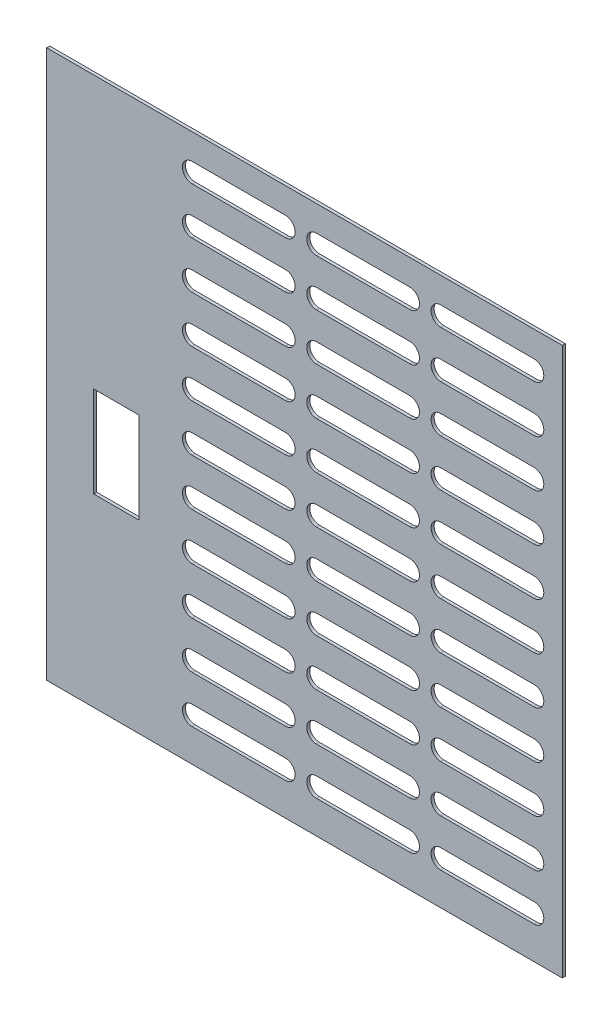
SolidWorks part; units mm, degrees
ref_plane "Plano frontal" through (0, 0, 0) normal (0, 0, 1) x (1, 0, 0)
ref_plane "Plano superior" through (0, 0, 0) normal (0, 1, 0) x (1, 0, 0)
ref_plane "Plano direito" through (0, 0, 0) normal (1, 0, 0) x (0, 0, -1)
sketch "Esboço1" plane through (0, 0, 0) normal (0, 0, 1) x (1, 0, 0)
  line L0 (-116.056, 178.9748) -> (-85.2858, 178.9748) construction
  line L1 (-205, 190.6547) -> (-35, 190.6547)
  line L2 (-205, 190.6547) -> (-205, 10)
  line L3 (-205, 10) -> (-35, 10)
  line L4 (-35, 190.6547) -> (-35, 10)
  line L5 (-116.056, 182.1711) -> (-85.2858, 182.1711)
  line L6 (-116.056, 175.7786) -> (-85.2858, 175.7786)
  line L7 (-75.056, 178.9748) -> (-44.2858, 178.9748) construction
  line L8 (-75.056, 182.1711) -> (-44.2858, 182.1711)
  line L9 (-157.056, 178.9748) -> (-126.2858, 178.9748) construction
  line L10 (-157.056, 182.1711) -> (-126.2858, 182.1711)
  line L11 (-157.056, 175.7786) -> (-126.2858, 175.7786)
  line L12 (-75.056, 175.7786) -> (-44.2858, 175.7786)
  line L13 (-116.056, 163.4748) -> (-85.2858, 163.4748) construction
  line L14 (-116.056, 166.6711) -> (-85.2858, 166.6711)
  line L15 (-116.056, 160.2786) -> (-85.2858, 160.2786)
  line L16 (-75.056, 163.4748) -> (-44.2858, 163.4748) construction
  line L17 (-75.056, 166.6711) -> (-44.2858, 166.6711)
  line L18 (-75.056, 160.2786) -> (-44.2858, 160.2786)
  line L19 (-116.056, 147.9748) -> (-85.2858, 147.9748) construction
  line L20 (-116.056, 151.1711) -> (-85.2858, 151.1711)
  line L21 (-116.056, 144.7786) -> (-85.2858, 144.7786)
  line L22 (-75.056, 147.9748) -> (-44.2858, 147.9748) construction
  line L23 (-75.056, 151.1711) -> (-44.2858, 151.1711)
  line L24 (-75.056, 144.7786) -> (-44.2858, 144.7786)
  line L25 (-116.056, 132.4748) -> (-85.2858, 132.4748) construction
  line L26 (-116.056, 135.6711) -> (-85.2858, 135.6711)
  line L27 (-116.056, 129.2786) -> (-85.2858, 129.2786)
  line L28 (-75.056, 132.4748) -> (-44.2858, 132.4748) construction
  line L29 (-75.056, 135.6711) -> (-44.2858, 135.6711)
  line L30 (-75.056, 129.2786) -> (-44.2858, 129.2786)
  line L31 (-116.056, 116.9748) -> (-85.2858, 116.9748) construction
  line L32 (-116.056, 120.1711) -> (-85.2858, 120.1711)
  line L33 (-116.056, 113.7786) -> (-85.2858, 113.7786)
  line L34 (-75.056, 116.9748) -> (-44.2858, 116.9748) construction
  line L35 (-75.056, 120.1711) -> (-44.2858, 120.1711)
  line L36 (-75.056, 113.7786) -> (-44.2858, 113.7786)
  line L37 (-116.056, 101.4748) -> (-85.2858, 101.4748) construction
  line L38 (-116.056, 104.6711) -> (-85.2858, 104.6711)
  line L39 (-116.056, 98.2786) -> (-85.2858, 98.2786)
  line L40 (-75.056, 101.4748) -> (-44.2858, 101.4748) construction
  line L41 (-75.056, 104.6711) -> (-44.2858, 104.6711)
  line L42 (-75.056, 98.2786) -> (-44.2858, 98.2786)
  line L43 (-116.056, 85.9748) -> (-85.2858, 85.9748) construction
  line L44 (-116.056, 89.1711) -> (-85.2858, 89.1711)
  line L45 (-116.056, 82.7786) -> (-85.2858, 82.7786)
  line L46 (-75.056, 85.9748) -> (-44.2858, 85.9748) construction
  line L47 (-75.056, 89.1711) -> (-44.2858, 89.1711)
  line L48 (-75.056, 82.7786) -> (-44.2858, 82.7786)
  line L49 (-116.056, 70.4748) -> (-85.2858, 70.4748) construction
  line L50 (-116.056, 73.6711) -> (-85.2858, 73.6711)
  line L51 (-116.056, 67.2786) -> (-85.2858, 67.2786)
  line L52 (-75.056, 70.4748) -> (-44.2858, 70.4748) construction
  line L53 (-75.056, 73.6711) -> (-44.2858, 73.6711)
  line L54 (-75.056, 67.2786) -> (-44.2858, 67.2786)
  line L55 (-116.056, 54.9748) -> (-85.2858, 54.9748) construction
  line L56 (-116.056, 58.1711) -> (-85.2858, 58.1711)
  line L57 (-116.056, 51.7786) -> (-85.2858, 51.7786)
  line L58 (-75.056, 54.9748) -> (-44.2858, 54.9748) construction
  line L59 (-75.056, 58.1711) -> (-44.2858, 58.1711)
  line L60 (-75.056, 51.7786) -> (-44.2858, 51.7786)
  line L61 (-116.056, 39.4748) -> (-85.2858, 39.4748) construction
  line L62 (-116.056, 42.6711) -> (-85.2858, 42.6711)
  line L63 (-116.056, 36.2786) -> (-85.2858, 36.2786)
  line L64 (-75.056, 39.4748) -> (-44.2858, 39.4748) construction
  line L65 (-75.056, 42.6711) -> (-44.2858, 42.6711)
  line L66 (-75.056, 36.2786) -> (-44.2858, 36.2786)
  line L67 (-116.056, 23.9748) -> (-85.2858, 23.9748) construction
  line L68 (-116.056, 27.1711) -> (-85.2858, 27.1711)
  line L69 (-116.056, 20.7786) -> (-85.2858, 20.7786)
  line L70 (-75.056, 23.9748) -> (-44.2858, 23.9748) construction
  line L71 (-75.056, 27.1711) -> (-44.2858, 27.1711)
  line L72 (-75.056, 20.7786) -> (-44.2858, 20.7786)
  line L73 (-157.056, 163.4748) -> (-126.2858, 163.4748) construction
  line L74 (-157.056, 166.6711) -> (-126.2858, 166.6711)
  line L75 (-157.056, 160.2786) -> (-126.2858, 160.2786)
  line L76 (-157.056, 147.9748) -> (-126.2858, 147.9748) construction
  line L77 (-157.056, 151.1711) -> (-126.2858, 151.1711)
  line L78 (-157.056, 144.7786) -> (-126.2858, 144.7786)
  line L79 (-157.056, 132.4748) -> (-126.2858, 132.4748) construction
  line L80 (-157.056, 135.6711) -> (-126.2858, 135.6711)
  line L81 (-157.056, 129.2786) -> (-126.2858, 129.2786)
  line L82 (-157.056, 116.9748) -> (-126.2858, 116.9748) construction
  line L83 (-157.056, 120.1711) -> (-126.2858, 120.1711)
  line L84 (-157.056, 113.7786) -> (-126.2858, 113.7786)
  line L85 (-157.056, 101.4748) -> (-126.2858, 101.4748) construction
  line L86 (-157.056, 104.6711) -> (-126.2858, 104.6711)
  line L87 (-157.056, 98.2786) -> (-126.2858, 98.2786)
  line L88 (-157.056, 85.9748) -> (-126.2858, 85.9748) construction
  line L89 (-157.056, 89.1711) -> (-126.2858, 89.1711)
  line L90 (-157.056, 82.7786) -> (-126.2858, 82.7786)
  line L91 (-157.056, 70.4748) -> (-126.2858, 70.4748) construction
  line L92 (-157.056, 73.6711) -> (-126.2858, 73.6711)
  line L93 (-157.056, 67.2786) -> (-126.2858, 67.2786)
  line L94 (-157.056, 54.9748) -> (-126.2858, 54.9748) construction
  line L95 (-157.056, 58.1711) -> (-126.2858, 58.1711)
  line L96 (-157.056, 51.7786) -> (-126.2858, 51.7786)
  line L97 (-157.056, 39.4748) -> (-126.2858, 39.4748) construction
  line L98 (-157.056, 42.6711) -> (-126.2858, 42.6711)
  line L99 (-157.056, 36.2786) -> (-126.2858, 36.2786)
  line L100 (-157.056, 23.9748) -> (-126.2858, 23.9748) construction
  line L101 (-157.056, 27.1711) -> (-126.2858, 27.1711)
  line L102 (-157.056, 20.7786) -> (-126.2858, 20.7786)
  line L109 (-174.5008, 85.9748) -> (-174.5008, 70.9748)
  line L110 (-174.5008, 70.9748) -> (-189.5008, 70.9748)
  line L111 (-189.5008, 70.9748) -> (-189.5008, 100.9748)
  line L112 (-189.5008, 100.9748) -> (-174.5008, 100.9748)
  line L113 (-174.5008, 100.9748) -> (-174.5008, 85.9748)
  arc A0 (-157.056, 182.1711) -> (-157.056, 175.7786) centre (-157.056, 178.9748) ccw
  arc A1 (-126.2858, 175.7786) -> (-126.2858, 182.1711) centre (-126.2858, 178.9748) ccw
  arc A2 (-116.056, 182.1711) -> (-116.056, 175.7786) centre (-116.056, 178.9748) ccw
  arc A3 (-85.2858, 175.7786) -> (-85.2858, 182.1711) centre (-85.2858, 178.9748) ccw
  arc A4 (-75.056, 182.1711) -> (-75.056, 175.7786) centre (-75.056, 178.9748) ccw
  arc A5 (-44.2858, 175.7786) -> (-44.2858, 182.1711) centre (-44.2858, 178.9748) ccw
  arc A6 (-116.056, 166.6711) -> (-116.056, 160.2786) centre (-116.056, 163.4748) ccw
  arc A7 (-85.2858, 160.2786) -> (-85.2858, 166.6711) centre (-85.2858, 163.4748) ccw
  arc A8 (-75.056, 166.6711) -> (-75.056, 160.2786) centre (-75.056, 163.4748) ccw
  arc A9 (-44.2858, 160.2786) -> (-44.2858, 166.6711) centre (-44.2858, 163.4748) ccw
  arc A10 (-116.056, 151.1711) -> (-116.056, 144.7786) centre (-116.056, 147.9748) ccw
  arc A11 (-85.2858, 144.7786) -> (-85.2858, 151.1711) centre (-85.2858, 147.9748) ccw
  arc A12 (-75.056, 151.1711) -> (-75.056, 144.7786) centre (-75.056, 147.9748) ccw
  arc A13 (-44.2858, 144.7786) -> (-44.2858, 151.1711) centre (-44.2858, 147.9748) ccw
  arc A14 (-116.056, 135.6711) -> (-116.056, 129.2786) centre (-116.056, 132.4748) ccw
  arc A15 (-85.2858, 129.2786) -> (-85.2858, 135.6711) centre (-85.2858, 132.4748) ccw
  arc A16 (-75.056, 135.6711) -> (-75.056, 129.2786) centre (-75.056, 132.4748) ccw
  arc A17 (-44.2858, 129.2786) -> (-44.2858, 135.6711) centre (-44.2858, 132.4748) ccw
  arc A18 (-116.056, 120.1711) -> (-116.056, 113.7786) centre (-116.056, 116.9748) ccw
  arc A19 (-85.2858, 113.7786) -> (-85.2858, 120.1711) centre (-85.2858, 116.9748) ccw
  arc A20 (-75.056, 120.1711) -> (-75.056, 113.7786) centre (-75.056, 116.9748) ccw
  arc A21 (-44.2858, 113.7786) -> (-44.2858, 120.1711) centre (-44.2858, 116.9748) ccw
  arc A22 (-116.056, 104.6711) -> (-116.056, 98.2786) centre (-116.056, 101.4748) ccw
  arc A23 (-85.2858, 98.2786) -> (-85.2858, 104.6711) centre (-85.2858, 101.4748) ccw
  arc A24 (-75.056, 104.6711) -> (-75.056, 98.2786) centre (-75.056, 101.4748) ccw
  arc A25 (-44.2858, 98.2786) -> (-44.2858, 104.6711) centre (-44.2858, 101.4748) ccw
  arc A26 (-116.056, 89.1711) -> (-116.056, 82.7786) centre (-116.056, 85.9748) ccw
  arc A27 (-85.2858, 82.7786) -> (-85.2858, 89.1711) centre (-85.2858, 85.9748) ccw
  arc A28 (-75.056, 89.1711) -> (-75.056, 82.7786) centre (-75.056, 85.9748) ccw
  arc A29 (-44.2858, 82.7786) -> (-44.2858, 89.1711) centre (-44.2858, 85.9748) ccw
  arc A30 (-116.056, 73.6711) -> (-116.056, 67.2786) centre (-116.056, 70.4748) ccw
  arc A31 (-85.2858, 67.2786) -> (-85.2858, 73.6711) centre (-85.2858, 70.4748) ccw
  arc A32 (-75.056, 73.6711) -> (-75.056, 67.2786) centre (-75.056, 70.4748) ccw
  arc A33 (-44.2858, 67.2786) -> (-44.2858, 73.6711) centre (-44.2858, 70.4748) ccw
  arc A34 (-116.056, 58.1711) -> (-116.056, 51.7786) centre (-116.056, 54.9748) ccw
  arc A35 (-85.2858, 51.7786) -> (-85.2858, 58.1711) centre (-85.2858, 54.9748) ccw
  arc A36 (-75.056, 58.1711) -> (-75.056, 51.7786) centre (-75.056, 54.9748) ccw
  arc A37 (-44.2858, 51.7786) -> (-44.2858, 58.1711) centre (-44.2858, 54.9748) ccw
  arc A38 (-116.056, 42.6711) -> (-116.056, 36.2786) centre (-116.056, 39.4748) ccw
  arc A39 (-85.2858, 36.2786) -> (-85.2858, 42.6711) centre (-85.2858, 39.4748) ccw
  arc A40 (-75.056, 42.6711) -> (-75.056, 36.2786) centre (-75.056, 39.4748) ccw
  arc A41 (-44.2858, 36.2786) -> (-44.2858, 42.6711) centre (-44.2858, 39.4748) ccw
  arc A42 (-116.056, 27.1711) -> (-116.056, 20.7786) centre (-116.056, 23.9748) ccw
  arc A43 (-85.2858, 20.7786) -> (-85.2858, 27.1711) centre (-85.2858, 23.9748) ccw
  arc A44 (-75.056, 27.1711) -> (-75.056, 20.7786) centre (-75.056, 23.9748) ccw
  arc A45 (-44.2858, 20.7786) -> (-44.2858, 27.1711) centre (-44.2858, 23.9748) ccw
  arc A46 (-157.056, 166.6711) -> (-157.056, 160.2786) centre (-157.056, 163.4748) ccw
  arc A47 (-126.2858, 160.2786) -> (-126.2858, 166.6711) centre (-126.2858, 163.4748) ccw
  arc A48 (-157.056, 151.1711) -> (-157.056, 144.7786) centre (-157.056, 147.9748) ccw
  arc A49 (-126.2858, 144.7786) -> (-126.2858, 151.1711) centre (-126.2858, 147.9748) ccw
  arc A50 (-157.056, 135.6711) -> (-157.056, 129.2786) centre (-157.056, 132.4748) ccw
  arc A51 (-126.2858, 129.2786) -> (-126.2858, 135.6711) centre (-126.2858, 132.4748) ccw
  arc A52 (-157.056, 120.1711) -> (-157.056, 113.7786) centre (-157.056, 116.9748) ccw
  arc A53 (-126.2858, 113.7786) -> (-126.2858, 120.1711) centre (-126.2858, 116.9748) ccw
  arc A54 (-157.056, 104.6711) -> (-157.056, 98.2786) centre (-157.056, 101.4748) ccw
  arc A55 (-126.2858, 98.2786) -> (-126.2858, 104.6711) centre (-126.2858, 101.4748) ccw
  arc A56 (-157.056, 89.1711) -> (-157.056, 82.7786) centre (-157.056, 85.9748) ccw
  arc A57 (-126.2858, 82.7786) -> (-126.2858, 89.1711) centre (-126.2858, 85.9748) ccw
  arc A58 (-157.056, 73.6711) -> (-157.056, 67.2786) centre (-157.056, 70.4748) ccw
  arc A59 (-126.2858, 67.2786) -> (-126.2858, 73.6711) centre (-126.2858, 70.4748) ccw
  arc A60 (-157.056, 58.1711) -> (-157.056, 51.7786) centre (-157.056, 54.9748) ccw
  arc A61 (-126.2858, 51.7786) -> (-126.2858, 58.1711) centre (-126.2858, 54.9748) ccw
  arc A62 (-157.056, 42.6711) -> (-157.056, 36.2786) centre (-157.056, 39.4748) ccw
  arc A63 (-126.2858, 36.2786) -> (-126.2858, 42.6711) centre (-126.2858, 39.4748) ccw
  arc A64 (-157.056, 27.1711) -> (-157.056, 20.7786) centre (-157.056, 23.9748) ccw
  arc A65 (-126.2858, 20.7786) -> (-126.2858, 27.1711) centre (-126.2858, 23.9748) ccw
  point P9 (-100.6709, 178.9748)
  point P14 (-141.6709, 178.9748)
  point P23 (-59.6709, 178.9748)
  point P30 (-100.6709, 163.4748)
  point P37 (-59.6709, 163.4748)
  point P44 (-100.6709, 147.9748)
  point P51 (-59.6709, 147.9748)
  point P58 (-100.6709, 132.4748)
  point P65 (-59.6709, 132.4748)
  point P72 (-100.6709, 116.9748)
  point P79 (-59.6709, 116.9748)
  point P86 (-100.6709, 101.4748)
  point P93 (-59.6709, 101.4748)
  point P100 (-100.6709, 85.9748)
  point P107 (-59.6709, 85.9748)
  point P114 (-100.6709, 70.4748)
  point P121 (-59.6709, 70.4748)
  point P128 (-100.6709, 54.9748)
  point P135 (-59.6709, 54.9748)
  point P142 (-100.6709, 39.4748)
  point P149 (-59.6709, 39.4748)
  point P156 (-100.6709, 23.9748)
  point P163 (-59.6709, 23.9748)
  point P170 (-141.6709, 163.4748)
  point P177 (-141.6709, 147.9748)
  point P184 (-141.6709, 132.4748)
  point P191 (-141.6709, 116.9748)
  point P198 (-141.6709, 101.4748)
  point P205 (-141.6709, 85.9748)
  point P212 (-141.6709, 70.4748)
  point P219 (-141.6709, 54.9748)
  point P226 (-141.6709, 39.4748)
  point P233 (-141.6709, 23.9748)
  dimension "D1" = 3
  dimension "D2" = 11
extrude "Ressalto-extrusão1" add sketch "Esboço1" along normal blind 1
